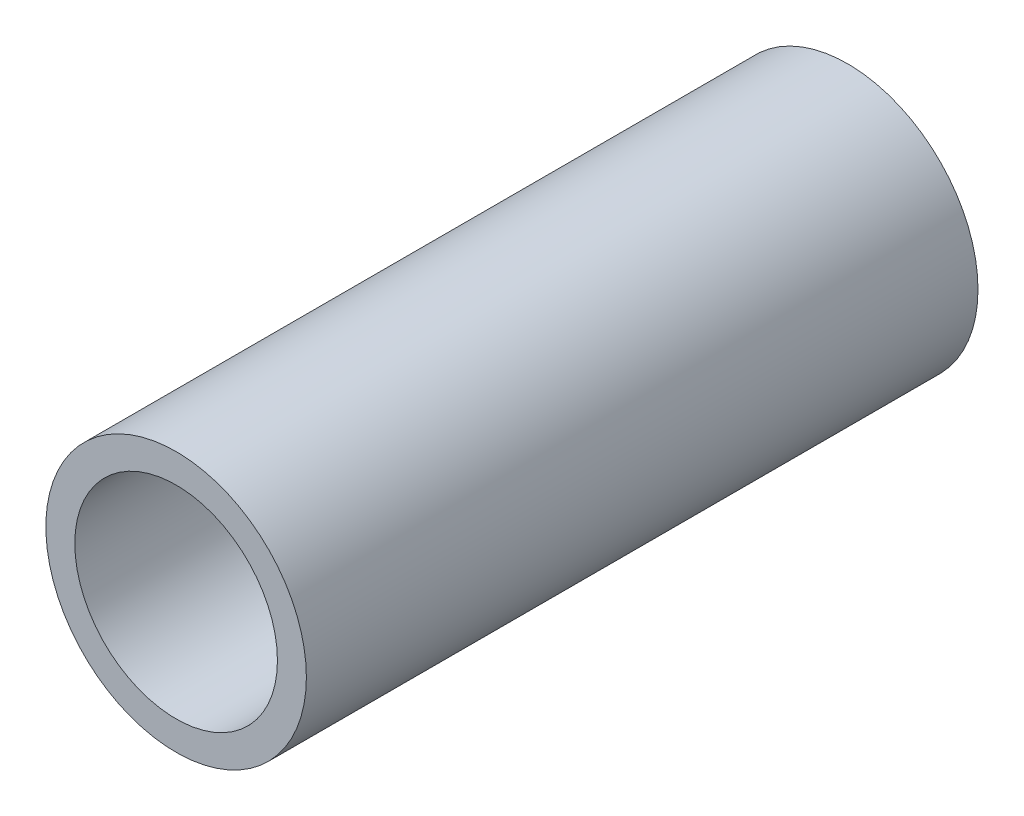
SolidWorks part; units mm, degrees
ref_plane "Plan de face" through (0, 0, 0) normal (0, 0, 1) x (1, 0, 0)
ref_plane "Plan de dessus" through (0, 0, 0) normal (0, 1, 0) x (1, 0, 0)
ref_plane "Plan de droite" through (0, 0, 0) normal (1, 0, 0) x (0, 0, -1)
sketch "Esquisse1" plane through (0, 0, 0) normal (0, 0, 1) x (1, 0, 0)
  circle A0 centre (0, 0) radius 4.375
  circle A1 centre (0, 0) radius 5.625
  dimension "D1" = 8.75
  dimension "D2" = 11.25
extrude "Extrusion1" add sketch "Esquisse1" along normal blind 29
